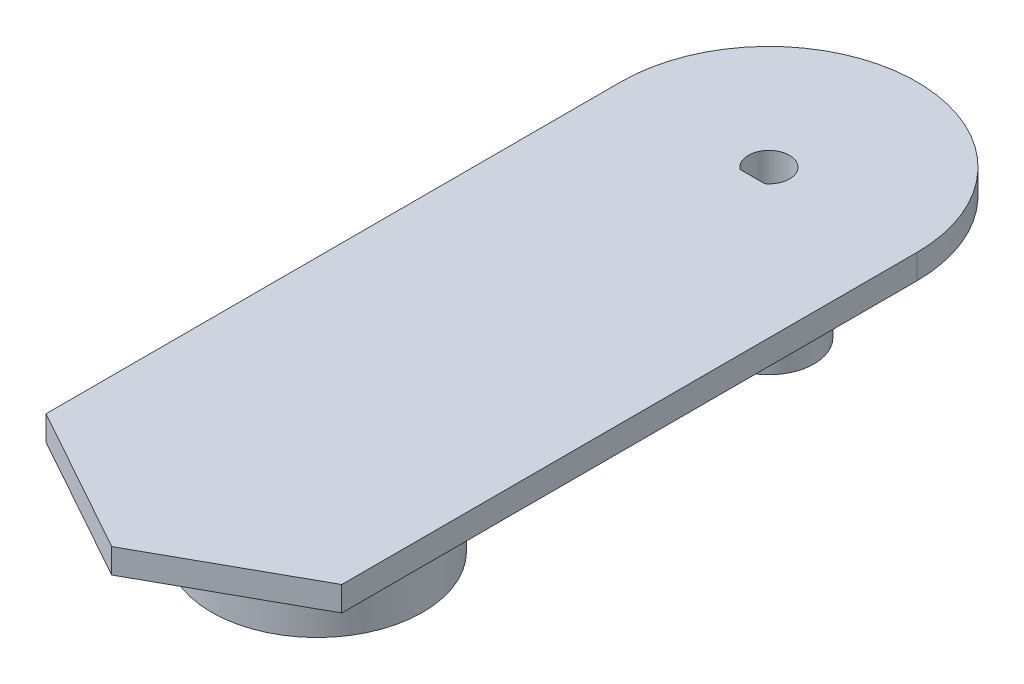
SolidWorks part; units mm, degrees
ref_plane "Front Plane" through (0, 0, 0) normal (0, 0, 1) x (1, 0, 0)
ref_plane "Top Plane" through (0, 0, 0) normal (0, 1, 0) x (1, 0, 0)
ref_plane "Right Plane" through (0, 0, 0) normal (1, 0, 0) x (0, 0, -1)
sketch "Sketch1" plane through (0, 0, 0) normal (0, 1, 0) x (1, 0, 0)
  line L0 (0, 0) -> (0, 5) construction
  line L1 (0, 5) -> (5, 5) construction
  line L2 (5, 5) -> (5, 0) construction
  line L3 (5, 0) -> (0, 0) construction
  line L4 (0, 0.5) -> (5, 0.5) construction
  line L5 (2.5, 0) -> (2.5, 5) construction
  line L6 (0, 2.5) -> (5, 2.5) construction
  line L7 (1, 0.5) -> (4, 0.5)
  circle A0 centre (2.5, 2.5) radius 2.5
  circle A1 centre (2.5, 2.5) radius 5.5
  dimension "D4" = 3
  dimension "D1" = 5
  dimension "D2" = 5
  dimension "D3" = 4.5
extrude "Boss-Extrude1" add sketch "Sketch1" along normal blind 15 contours A1 A0 | L7 A0
sketch "Sketch2" plane through (0, 15, 0) normal (0, 1, 0) x (1, 0, 0)
  line L0 (-3, 2.5) -> (8, 2.5) construction
  line L1 (2.5, 8) -> (2.5, -3) construction
  line L2 (-15.5, 2.5) -> (-15.5, -67.5)
  line L3 (20.5, 2.5) -> (20.5, -67.5)
  line L4 (-15.5, -67.5) -> (2.5, -77.5)
  line L5 (2.5, -77.5) -> (20.5, -67.5)
  line L8 (-25.5, -67.5) -> (30.5, -67.5) construction
  line L9 (2.5, 2.5) -> (2.5, -77.5) construction
  line L10 (-38, -77.5) -> (43, -77.5) construction
  circle A0 centre (2.5, 2.5) radius 5.5 construction
  circle A2 centre (2.5, 2.5) radius 18
  point P14 (33, 2.5)
  point P15 (-28, 2.5)
  point P17 (-28, -67.5)
  point P21 (33, -67.5)
  arc M6 (1, 0.5) -> (4, 0.5) centre (2.5, 2.5) cw
  line M7 (4, 0.5) -> (1, 0.5)
  circle M8 centre (2.5, 2.5) radius 5.5
  dimension "D1" = 12.5
  dimension "D2" = 10
  dimension "D3" = 10
  dimension "D4" = 10
  dimension "D5" = 80
extrude "Boss-Extrude3" add sketch "Sketch2" along normal blind 3 contours A2 M8 | M8 M7 M6 | A2 L2 L4 L5 L3
sketch "Sketch3" plane through (0, 15, 0) normal (0, -1, 0) x (1, 0, 0)
  line L0 (-15.5, 67.5) -> (20.5, 67.5) construction
  line L1 (2.5, 67.5) -> (2.5, -5) construction
  circle A0 centre (2.5, 52.5) radius 9.86
  circle A1 centre (2.5, 52.5) radius 12.86
  arc A2 (1, -0.5) -> (4, -0.5) centre (2.5, -2.5) ccw construction
  point P12 (2.5, 46.642)
  dimension "D1" = 19.72
  dimension "D2" = 3
  dimension "D3" = 15
extrude "Boss-Extrude4" add sketch "Sketch3" along normal blind 10
